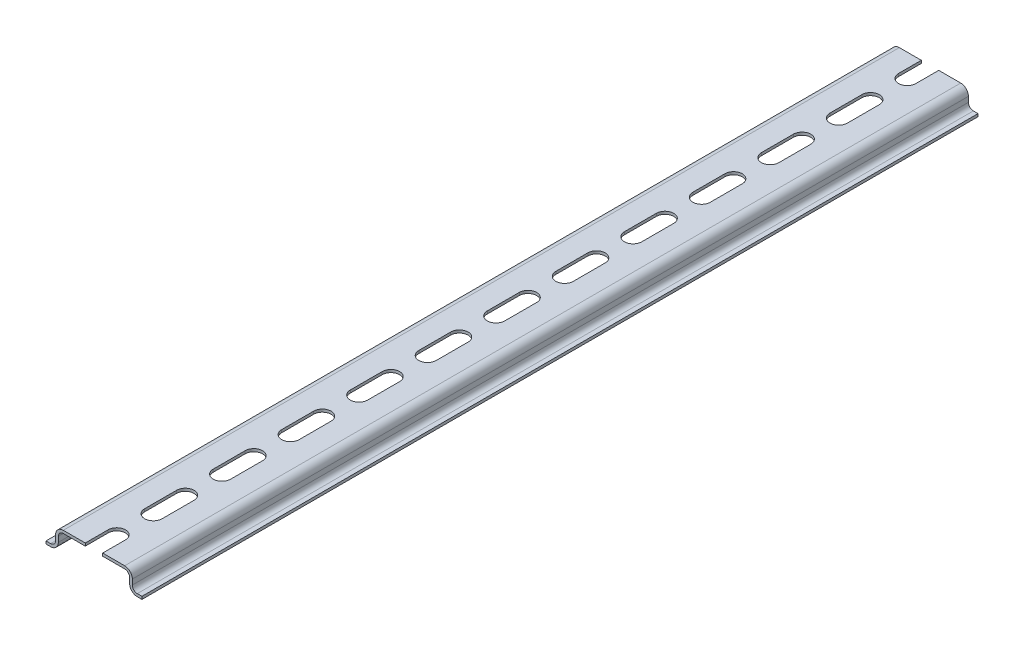
SolidWorks part; units mm, degrees
material "AISI 1020 Steel, Cold Rolled"
ref_plane "Front Plane" through (0, 0, 0) normal (0, 0, 1) x (1, 0, 0)
ref_plane "Top Plane" through (0, 0, 0) normal (0, 1, 0) x (1, 0, 0)
ref_plane "Right Plane" through (0, 0, 0) normal (1, 0, 0) x (0, 0, -1)
sketch "Sketch1" plane through (0, 0, 0) normal (0, 0, 1) x (1, 0, 0)
  line L0 (-17.5, 0.5) -> (-15.8, 0.5)
  line L13 (-13.5, 2.8) -> (-13.5, 4.7)
  line L14 (-11.2, 7) -> (11.2, 7)
  line L15 (0, 0) -> (0, 11.0461) construction
  line L16 (13.5, 2.8) -> (13.5, 4.7)
  line L17 (17.5, 0.5) -> (15.8, 0.5)
  arc A0 (-13.5, 2.8) -> (-15.8, 0.5) centre (-15.8, 2.8) cw
  arc A1 (-13.5, 4.7) -> (-11.2, 7) centre (-11.2, 4.7) cw
  arc A2 (13.5, 4.7) -> (11.2, 7) centre (11.2, 4.7) ccw
  arc A3 (13.5, 2.8) -> (15.8, 0.5) centre (15.8, 2.8) ccw
  point P17 (0, 7)
  dimension "D4" = 2.3
  dimension "D1" = 35
  dimension "D2" = 27
  dimension "D3" = 6.5
  dimension "D5" = 0.5
extrude "Extrude_main" add sketch "Sketch1" along normal mid plane 305 thin contours L0 A0 L13 A1 L14 A2 L16 A3 L17 thin type mid plane wall 1
sketch "Sketch2" plane through (0, 0, 0) normal (0, 1, 0) x (1, 0, 0)
  line L0 (-3.175, 5.825) -> (-3.175, -5.825)
  line L1 (3.175, 5.825) -> (3.175, -5.825)
  line L2 (0, 5.825) -> (0, -5.825) construction
  line L3 (-3.175, 5.825) -> (3.175, 5.825) construction
  line L4 (-3.175, -5.825) -> (3.175, -5.825) construction
  arc A0 (3.175, 5.825) -> (-3.175, 5.825) centre (0, 5.825) ccw
  arc A1 (-3.175, -5.825) -> (3.175, -5.825) centre (0, -5.825) ccw
  point P3 (0, 9)
  point P7 (0, -9)
  point P8 (0, 0)
  dimension "D1" = 6.35
  dimension "D2" = 18
extrude "slot_cut" cut sketch "Sketch2" along normal through all
pattern_linear "slot_pattern" count 7 spacing 25 along (0, 0, 1) count 7 spacing 25 along (0, 0, -1) of "slot_cut"
equation "\"LENGTH\"= 305mm"
equation "\"D1@Extrude_main\" = \"LENGTH\""
equation "\"D5@Sketch1\"=0.5"
